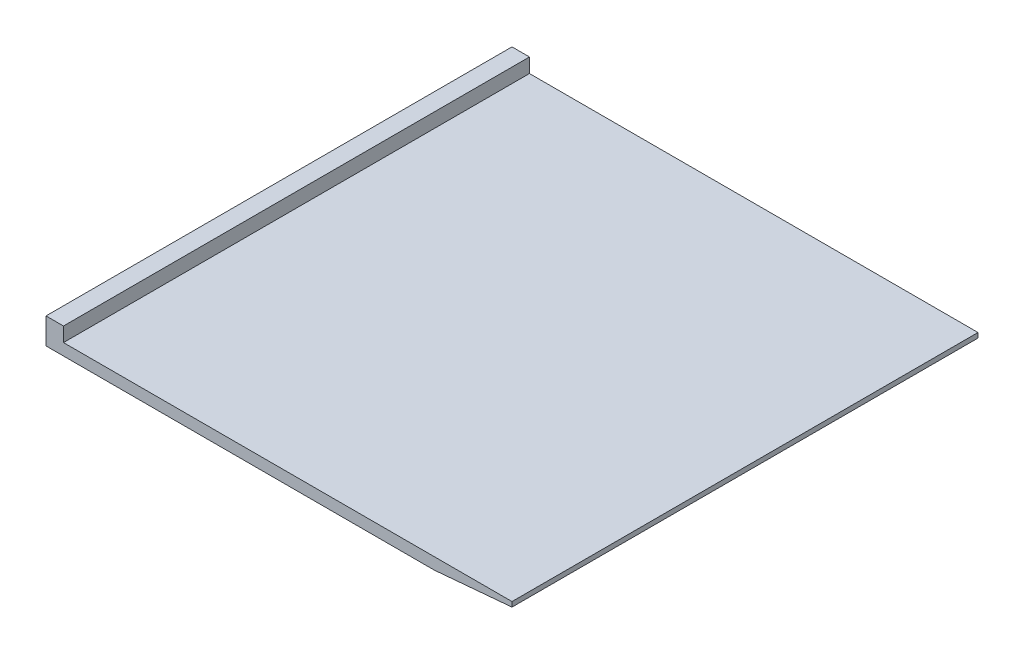
SolidWorks part; units mm, degrees
ref_plane "Front Plane" through (0, 0, 0) normal (0, 0, 1) x (1, 0, 0)
ref_plane "Top Plane" through (0, 0, 0) normal (0, 1, 0) x (1, 0, 0)
ref_plane "Right Plane" through (0, 0, 0) normal (1, 0, 0) x (0, 0, -1)
sketch "Sketch1" plane through (0, 0, 0) normal (0, 1, 0) x (1, 0, 0)
  line L0 (-15, 30) -> (-15, -30) construction
  line L1 (-30, -30) -> (30, -30)
  line L2 (-30, -30) -> (-30, 30)
  line L3 (-30, 30) -> (30, 30)
  line L4 (30, -30) -> (30, 30)
  line L5 (-30, -30) -> (30, 30) construction
  line L6 (-30, 30) -> (30, -30) construction
  line L7 (0, 30) -> (0, -30) construction
  line L8 (15, 30) -> (15, -30) construction
  line L9 (-30, 15) -> (30, 15) construction
  line L10 (-30, 0) -> (30, 0) construction
  line L11 (-30, -15) -> (30, -15) construction
  point P0 (0, 0)
  dimension "D1" = 15
  dimension "D2" = 60
  dimension "D4" = 15
  dimension "D3" = 3
  dimension "D5" = 3
extrude "Boss-Extrude1" add sketch "Sketch1" along normal blind 1.5
sketch "Sketch4" plane through (0, 1.5, 0) normal (0, 1, 0) x (1, 0, 0)
  line L0 (-30, -30) -> (30, -30) construction
  line L1 (-30, 30) -> (-27.75, 30)
  line L2 (-30, 30) -> (-30, -30)
  line L3 (-30, -30) -> (-27.75, -30)
  line L4 (-27.75, 30) -> (-27.75, -30)
  dimension "D1" = 2.25
extrude "Boss-Extrude2" add sketch "Sketch4" along normal blind 1.85
chamfer "Chamfer1" distance 10 angle 5 1 edges at (30, 0, 0)
